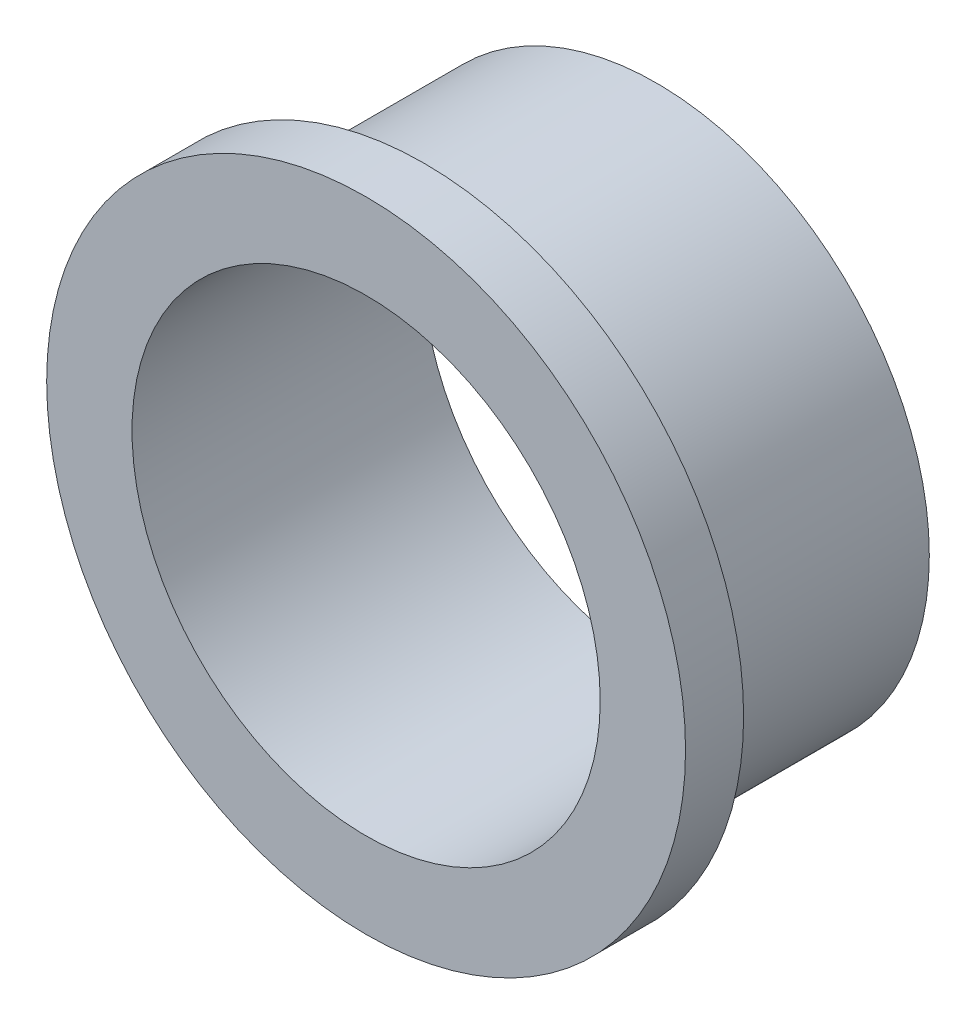
SolidWorks part; units mm, degrees
ref_plane "Plane1" through (0, 0, 0) normal (0, 0, 1) x (1, 0, 0)
ref_plane "Plane2" through (0, 0, 0) normal (0, 1, 0) x (1, 0, 0)
ref_plane "Plane3" through (0, 0, 0) normal (1, 0, 0) x (0, 0, -1)
sketch "Sketch5" plane through (0, 0, 0) normal (0, 1, 0) x (-1, 0, 0)
  line L0 (-7.1586, -6.096) -> (-6.1426, -6.096)
  line L2 (-6.1426, -6.096) -> (-6.1426, 1.524)
  line L3 (-6.1426, 1.524) -> (-8.382, 1.524)
  line L4 (-8.382, 1.524) -> (-8.382, 0)
  line L5 (10.414, 0) -> (-10.414, 0) construction
  line L6 (-7.1586, 0) -> (-7.1586, -6.096)
  line L7 (0, 0) -> (0, -6.096) construction
  line L9 (0, -34.925) -> (0, 0) construction
  line L10 (-7.1586, 0) -> (-8.382, 0)
  line L11 (-7.1586, 0) -> (-8.001, -48.26) construction
  dimension "D1" = 8.382
  dimension "D2" = 1.524
  dimension "D3" = 1.016
  dimension "D4" = 7.62
revolve "Base-Revolve" add sketch "Sketch5" angle 360 about L7
